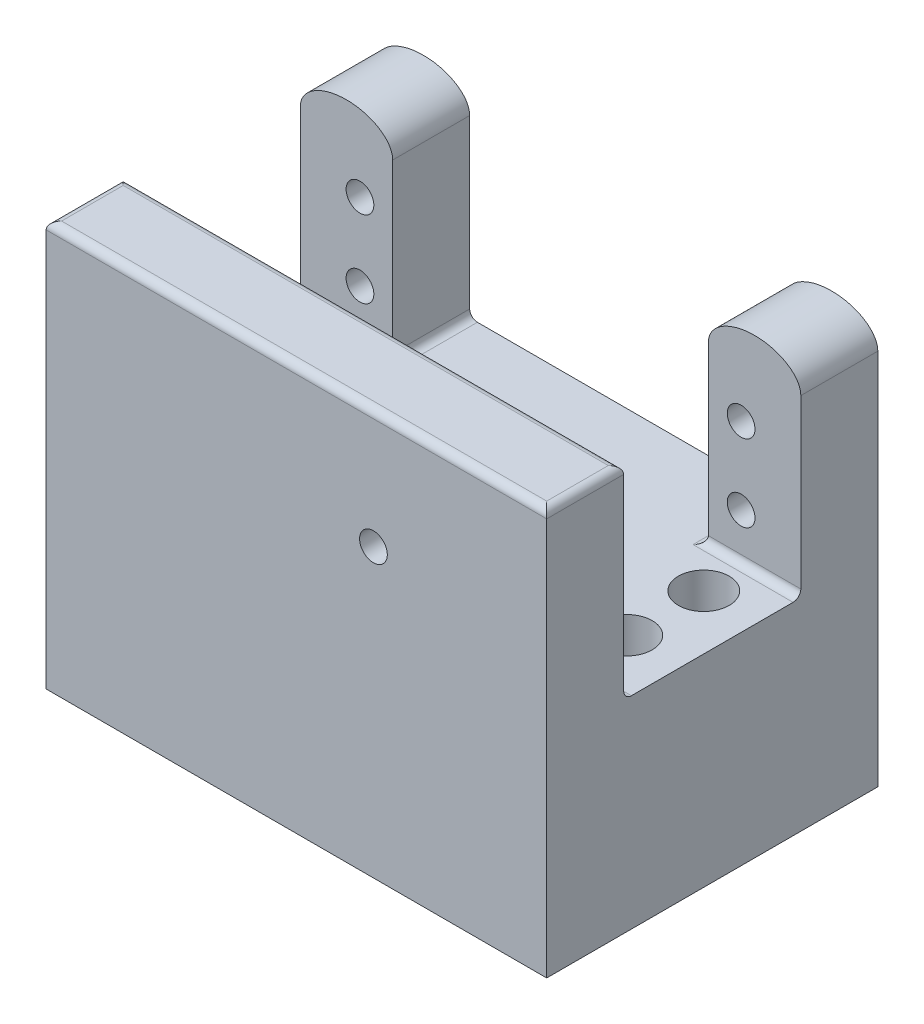
SolidWorks part; units mm, degrees
ref_plane "Front Plane" through (0, 0, 0) normal (0, 0, 1) x (1, 0, 0)
ref_plane "Top Plane" through (0, 0, 0) normal (0, 1, 0) x (1, 0, 0)
ref_plane "Right Plane" through (0, 0, 0) normal (1, 0, 0) x (0, 0, -1)
sketch "Sketch1" plane through (0, 0, 0) normal (0, 0, 1) x (1, 0, 0)
  line L0 (0, 25.9884) -> (0, -27.0349) construction
  line L1 (-6, 14.3023) -> (-6, -20.6977)
  line L2 (6, 14.3023) -> (6, -20.6977)
  line L3 (-6, -20.6977) -> (6, -20.6977)
  ellipse E0 centre (0, 14.3023) end of major axis (6, 14.3023) minor radius 3.7757 (6, 14.3023) -> (-6, 14.3023) ccw
  point P8 (-15.3172, 25.9959)
  dimension "D1" = 35
  dimension "D2" = 12
extrude "Boss-Extrude1" add sketch "Sketch1" along normal blind 10
sketch "Sketch2" plane through (0, 0, 10) normal (0, 0, 1) x (1, 0, 0)
  line L0 (6, -20.6977) -> (6, 14.3023) construction
  line L1 (-6, -20.6977) -> (6, -20.6977)
  line L2 (-6, -20.6977) -> (-6, -8.4477)
  line L3 (-6, -8.4477) -> (6, -8.4477)
  line L4 (6, -20.6977) -> (6, -8.4477)
  dimension "D1" = 12.25
extrude "Boss-Extrude2" add sketch "Sketch2" along normal blind 23 contours L3 L4 L1 L2
sketch "Sketch4" plane through (0, 0, 33) normal (0, 0, 1) x (1, 0, 0)
  line L1 (6, -20.6977) -> (-59, -20.6977)
  line L2 (6, -20.6977) -> (6, 17.9393)
  line L3 (6, 17.9393) -> (-59, 17.9393)
  line L4 (-59, -20.6977) -> (-59, 17.9393)
  dimension "D1" = 65
extrude "Boss-Extrude3" add sketch "Sketch4" along normal blind 10
ref_plane "Plane1" through (-26.5, 0, 0) normal (-1, 0, 0) x (0, 0, 1)
sketch "Sketch11" plane through (0, 0, 0) normal (0, 0, -1) x (-1, 0, 0)
  circle A0 centre (51.25, 8) radius 1.5
  circle A1 centre (51.25, -2) radius 1.5
  circle A3 centre (1.75, 7.5522) radius 1.5
  circle A4 centre (1.75, -2.4478) radius 1.5
  dimension "D1" = 49.5
  dimension "D4" = 3
  dimension "D5" = 3
  dimension "D6" = 3
  dimension "D7" = 3
  dimension "D2" = 10
  dimension "D3" = 49.5
  dimension "D8" = 10
mirror "Mirror2" about plane through (-26.5, 0, 0) normal (-1, 0, 0) of "Boss-Extrude2"
mirror "Mirror3" about plane through (-26.5, 0, 0) normal (-1, 0, 0) of "Boss-Extrude1"
hole_wizard "Ø3.6 (3.6) Diameter Hole1" positions "Sketch14" profile "Sketch15" hole size "Ø3.6" standard "ANSI Metric"
sketch "Sketch14" plane through (0, 0, 0) normal (0, 0, -1) x (-1, 0, 0)
  point P0 (1.75, 7.5522)
  point P3 (1.75, -2.4478)
  point P6 (51.25, 8)
  point P9 (51.25, -2)
sketch "Sketch15" plane through (-1.75, 7.5522, 0) normal (1, 0, 0) x (0, 1, 0)
  line L0 (0, 0) -> (0, 11.0815)
  line L1 (0, 11.0815) -> (1.8, 10)
  line L2 (1.8, 10) -> (1.8, 0)
  line L5 (1.8, 0) -> (0, 0)
  line L10 (0, 11.0815) -> (-1.8, 10) construction
  line L11 (0, -6.35) -> (0, 107.95) construction
  dimension "Hole Dia." = 3.6
  dimension "Hole Depth" = 10
  dimension "Drill Angle" = 118
sketch "Sketch21" plane through (0, 0, 33) normal (0, 0, -1) x (-1, 0, 0)
  line L1 (6, -8.4477) -> (47, -8.4477)
  line L2 (6, -8.4477) -> (6, -20.6977)
  line L3 (6, -20.6977) -> (47, -20.6977)
  line L4 (47, -8.4477) -> (47, -20.6977)
extrude "Boss-Extrude4" add sketch "Sketch21" along normal up to surface (33 mm away) up to face at (-3.55, 7.5522, 0)
sketch "Sketch23" plane through (0, -20.6977, 0) normal (0, -1, 0) x (1, 0, 0)
  line L1 (-59, 43) -> (6, 43)
  line L2 (-59, 43) -> (-59, 0)
  line L3 (-59, 0) -> (6, 0)
  line L4 (6, 43) -> (6, 0)
extrude "Boss-Extrude6" add sketch "Sketch23" along normal blind 14
sketch "Sketch24" plane through (0, -34.6977, 0) normal (0, -1, 0) x (-1, 0, 0)
  line L6 (-6, 0) -> (-6, -43) construction
  circle A0 centre (1.1, -25.5) radius 3
  circle A2 centre (51.9, -25.5) radius 3
  circle A4 centre (1.1, -15.5) radius 3
  circle A5 centre (51.9, -15.5) radius 3
  dimension "D4" = 6
  dimension "D5" = 6
  dimension "D1" = 10
  dimension "D2" = 10
  dimension "D8" = 7.1
fillet "Fillet1" radius 1 9 edges at (-26.5, 17.9393, 43) (-26.5, 17.9393, 33) (6, 17.9393, 38) (-59, 17.9393, 38) (-53, -8.4477, 10) (0, -8.4477, 10) (-6, -8.4477, 5) (-47, -8.4477, 5) (-26.5, -8.4477, 33)
hole_wizard "Ø6.6 (6.6) Diameter Hole1" positions "Sketch25" profile "Sketch26" hole size "Ø6.6" standard "ANSI Metric" end condition through all
sketch "Sketch25" plane through (0, -34.6977, 0) normal (0, -1, 0) x (-1, 0, 0)
  point P0 (1.1, -15.5)
  point P3 (1.1, -25.5)
  point P6 (51.9, -15.5)
  point P9 (51.9, -25.5)
sketch "Sketch26" plane through (-1.1, -34.6977, 15.5) normal (1, 0, 0) x (0, 0, -1)
  line L0 (0, 0) -> (0, 52.7757)
  line L1 (0, 52.7757) -> (3.3, 52.7757)
  line L2 (3.3, 52.7757) -> (3.3, 0)
  line L5 (3.3, 0) -> (0, 0)
  line L11 (0, -6.35) -> (0, 107.95) construction
  dimension "Thru Hole Dia." = 6.6
  dimension "Thru Hole Depth" = 52.7757
sketch "Sketch28" plane through (0, 0, 43) normal (0, 0, 1) x (1, 0, 0)
  circle A2 centre (-16.5, 2.553) radius 1.8
extrude "Cut-Extrude1" cut sketch "Sketch28" against normal through all
